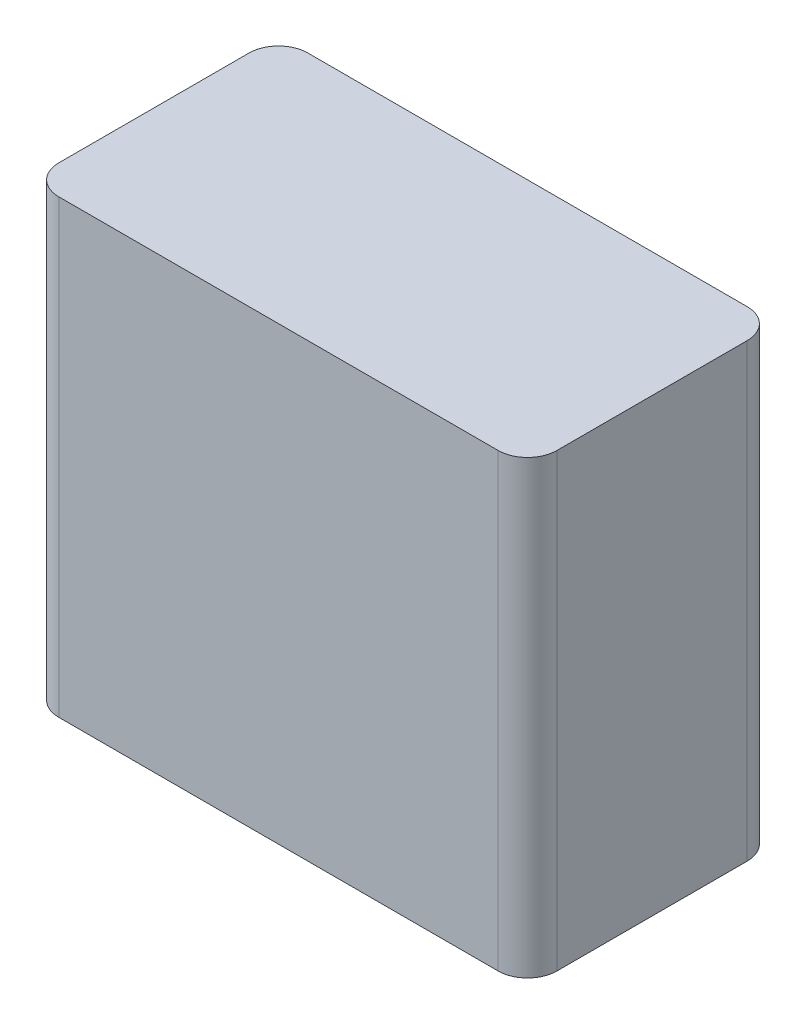
SolidWorks part; units mm, degrees
ref_plane "Front Plane" through (0, 0, 0) normal (0, 0, 1) x (1, 0, 0)
ref_plane "Top Plane" through (0, 0, 0) normal (0, 1, 0) x (1, 0, 0)
ref_plane "Right Plane" through (0, 0, 0) normal (1, 0, 0) x (0, 0, -1)
sketch "Sketch1" plane through (0, 0, 0) normal (0, 1, 0) x (1, 0, 0)
  line L1 (20, -10) -> (-20, -10)
  line L2 (20, -10) -> (20, 10)
  line L3 (20, 10) -> (-20, 10)
  line L4 (-20, -10) -> (-20, 10)
  line L5 (20, -10) -> (-20, 10) construction
  line L6 (20, 10) -> (-20, -10) construction
  point P0 (0, 0)
  dimension "D1" = 40
  dimension "D2" = 20
extrude "Boss-Extrude1" add sketch "Sketch1" along normal blind 36.2
fillet "Fillet1" radius 2.36 4 edges at (-20, 18.1, -10) (20, 18.1, -10) (-20, 18.1, 10) (20, 18.1, 10)
